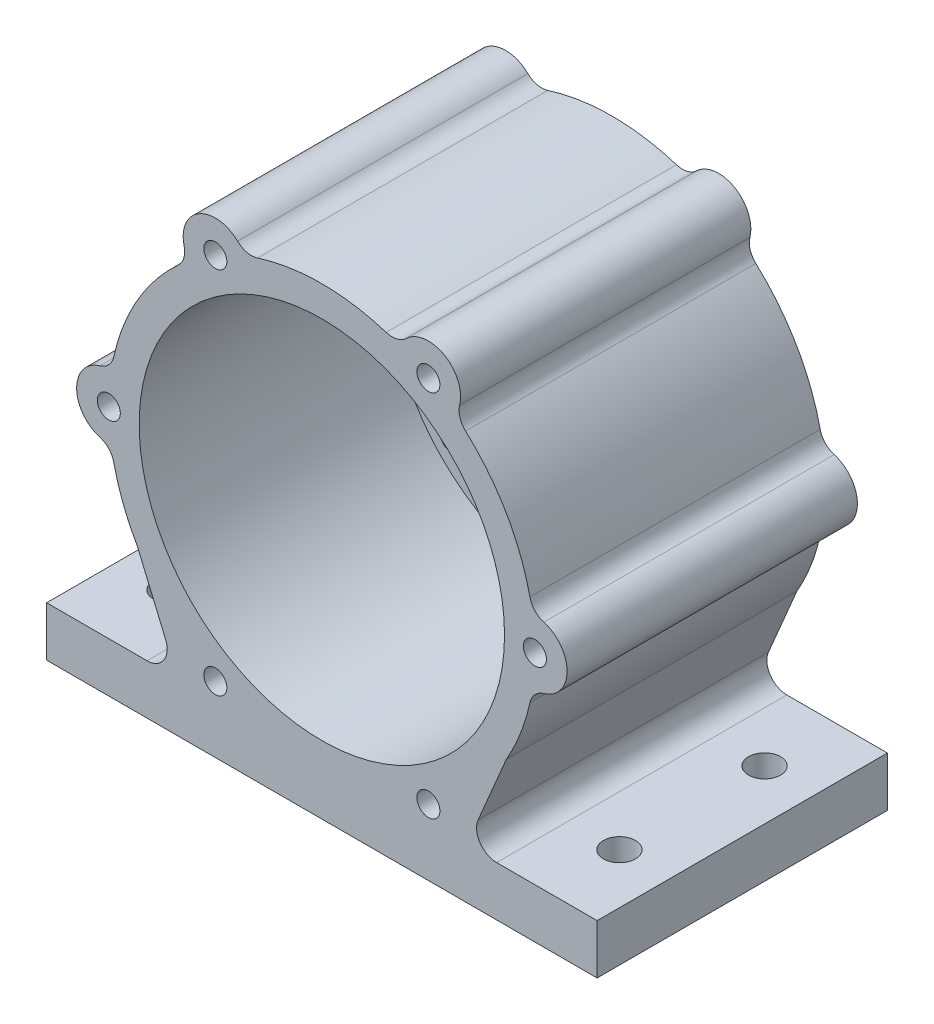
SolidWorks part; units mm, degrees
ref_plane "Front Plane" through (0, 0, 0) normal (0, 0, 1) x (1, 0, 0)
ref_plane "Top Plane" through (0, 0, 0) normal (0, 1, 0) x (1, 0, 0)
ref_plane "Right Plane" through (0, 0, 0) normal (1, 0, 0) x (0, 0, -1)
sketch "Sketch1" plane through (0, 0, 0) normal (0, 0, 1) x (1, 0, 0)
  line L0 (0, 0) -> (10.6425, 18.4334) construction
  line L1 (0, 0) -> (18.25, 0) construction
  circle A0 centre (0, 0) radius 21.285 construction
  circle A1 centre (0, 0) radius 18.25
  circle A2 centre (0, 0) radius 24.5
  circle A3 centre (10.6425, 18.4334) radius 1.15
  circle A4 centre (21.285, 0) radius 1.15
  circle A5 centre (10.6425, -18.4334) radius 1.15
  circle A6 centre (-10.6425, -18.4334) radius 1.15
  circle A7 centre (-21.285, 0) radius 1.15
  circle A8 centre (-10.6425, 18.4334) radius 1.15
  point P19 (0, 0)
  dimension "D1" = 49
  dimension "D2" = 36.5
  dimension "D3" = 42.57
  dimension "D4" = 2.3
  dimension "D6" = 60
  dimension "D5" = 6
extrude "Shell" add sketch "Sketch1" along normal blind 25
sketch "Sketch2" plane through (0, 0, 0) normal (0, 0, -1) x (-1, 0, 0)
  circle A0 centre (0, 0) radius 24.5 construction
  circle A1 centre (0, 0) radius 24.5
  circle A2 centre (0, 0) radius 7.25
  dimension "D1" = 14.5
extrude "Front Face" add sketch "Sketch2" along normal blind 4
sketch "Sketch3" plane through (0, 0, 0) normal (0, 0, 1) x (1, 0, 0)
  line L0 (2.9546, 10.8086) -> (4.278, 15.6446)
  line L1 (-3.0208, 10.8073) -> (-4.2915, 15.6527)
  line L2 (0, 0) -> (0, 17.25) construction
  line L3 (0, 17.25) -> (4.5502, 16.6391) construction
  line L4 (0, 17.25) -> (-4.5502, 16.6391) construction
  line L5 (10.8379, 2.8455) -> (15.6877, 4.1174)
  line L6 (7.849, 8.0197) -> (11.4099, 11.5429)
  line L7 (14.9389, 8.625) -> (16.6849, 4.379) construction
  line L8 (14.9389, 8.625) -> (12.1348, 12.2601) construction
  line L9 (7.8832, -7.9631) -> (11.4096, -11.5272)
  line L10 (10.8698, -2.7876) -> (15.7014, -4.1098)
  line L11 (14.9389, -8.625) -> (12.1348, -12.2601) construction
  line L12 (14.9389, -8.625) -> (16.6849, -4.379) construction
  line L13 (-2.9546, -10.8086) -> (-4.278, -15.6446)
  line L14 (3.0208, -10.8073) -> (4.2915, -15.6527)
  line L15 (0, -17.25) -> (-4.5502, -16.6391) construction
  line L16 (0, -17.25) -> (4.5502, -16.6391) construction
  line L17 (-10.8379, -2.8455) -> (-15.6877, -4.1174)
  line L18 (-7.849, -8.0197) -> (-11.4099, -11.5429)
  line L19 (-14.9389, -8.625) -> (-16.6849, -4.379) construction
  line L20 (-14.9389, -8.625) -> (-12.1348, -12.2601) construction
  line L21 (-7.8832, 7.9631) -> (-11.4096, 11.5272)
  line L22 (-10.8698, 2.7876) -> (-15.7014, 4.1098)
  line L23 (-14.9389, 8.625) -> (-12.1348, 12.2601) construction
  line L24 (-14.9389, 8.625) -> (-16.6849, 4.379) construction
  arc A0 (3.5174, 16.8876) -> (-3.5288, 16.8852) centre (0, 0) ccw
  arc A1 (1.8132, 10.0883) -> (-1.8709, 10.0778) centre (0, 0) ccw
  arc A2 (-3.0208, 10.8073) -> (-1.8709, 10.0778) centre (-2.0535, 11.061) ccw
  arc A3 (2.9546, 10.8086) -> (1.8132, 10.0883) centre (1.9901, 11.0726) cw
  arc A4 (4.278, 15.6446) -> (3.5174, 16.8876) centre (3.3135, 15.9086) ccw
  arc A5 (-4.2915, 15.6527) -> (-3.5288, 16.8852) centre (-3.3242, 15.9064) cw
  circle A6 centre (0, 0) radius 7.25 construction
  circle A7 centre (0, 0) radius 18.25 construction
  arc A8 (16.3838, 5.3976) -> (12.8586, 11.4986) centre (0, 0) ccw
  arc A9 (9.6434, 3.4739) -> (7.7922, 6.6592) centre (0, 0) ccw
  arc A10 (7.849, 8.0197) -> (7.7922, 6.6592) centre (8.5524, 7.3089) ccw
  arc A11 (10.8379, 2.8455) -> (9.6434, 3.4739) centre (10.5842, 3.8128) cw
  arc A12 (15.6877, 4.1174) -> (16.3838, 5.3976) centre (15.434, 5.0847) ccw
  arc A13 (11.4099, 11.5429) -> (12.8586, 11.4986) centre (12.1132, 10.832) cw
  arc A14 (12.8664, -11.49) -> (16.3874, -5.3866) centre (0, 0) ccw
  arc A15 (7.8302, -6.6145) -> (9.6631, -3.4186) centre (0, 0) ccw
  arc A16 (10.8698, -2.7876) -> (9.6631, -3.4186) centre (10.6058, -3.7521) ccw
  arc A17 (7.8832, -7.9631) -> (7.8302, -6.6145) centre (8.5941, -7.2598) cw
  arc A18 (11.4096, -11.5272) -> (12.8664, -11.49) centre (12.1205, -10.8239) ccw
  arc A19 (15.7014, -4.1098) -> (16.3874, -5.3866) centre (15.4374, -5.0743) cw
  arc A20 (-3.5174, -16.8876) -> (3.5288, -16.8852) centre (0, 0) ccw
  arc A21 (-1.8132, -10.0883) -> (1.8709, -10.0778) centre (0, 0) ccw
  arc A22 (3.0208, -10.8073) -> (1.8709, -10.0778) centre (2.0535, -11.061) ccw
  arc A23 (-2.9546, -10.8086) -> (-1.8132, -10.0883) centre (-1.9901, -11.0726) cw
  arc A24 (-4.278, -15.6446) -> (-3.5174, -16.8876) centre (-3.3135, -15.9086) ccw
  arc A25 (4.2915, -15.6527) -> (3.5288, -16.8852) centre (3.3242, -15.9064) cw
  arc A26 (-16.3838, -5.3976) -> (-12.8586, -11.4986) centre (0, 0) ccw
  arc A27 (-9.6434, -3.4739) -> (-7.7922, -6.6592) centre (0, 0) ccw
  arc A28 (-7.849, -8.0197) -> (-7.7922, -6.6592) centre (-8.5524, -7.3089) ccw
  arc A29 (-10.8379, -2.8455) -> (-9.6434, -3.4739) centre (-10.5842, -3.8128) cw
  arc A30 (-15.6877, -4.1174) -> (-16.3838, -5.3976) centre (-15.434, -5.0847) ccw
  arc A31 (-11.4099, -11.5429) -> (-12.8586, -11.4986) centre (-12.1132, -10.832) cw
  arc A32 (-12.8664, 11.49) -> (-16.3874, 5.3866) centre (0, 0) ccw
  arc A33 (-7.8302, 6.6145) -> (-9.6631, 3.4186) centre (0, 0) ccw
  arc A34 (-10.8698, 2.7876) -> (-9.6631, 3.4186) centre (-10.6058, 3.7521) ccw
  arc A35 (-7.8832, 7.9631) -> (-7.8302, 6.6145) centre (-8.5941, 7.2598) cw
  arc A36 (-11.4096, 11.5272) -> (-12.8664, 11.49) centre (-12.1205, 10.8239) ccw
  arc A37 (-15.7014, 4.1098) -> (-16.3874, 5.3866) centre (-15.4374, 5.0743) cw
  point P98 (0, 0)
  dimension "D2" = 1
  dimension "D3" = 3
  dimension "D4" = 1
  dimension "D1" = 30
  dimension "D5" = 6
extrude "Front Cutout" cut sketch "Sketch3" against normal up to next
sketch "Sketch4" plane through (0, 0, 25) normal (0, 0, 1) x (1, 0, 0)
  arc A0 (-14.3579, 15.7131) -> (-20.7869, 4.5777) centre (0, 0) ccw
  arc A1 (-8.4173, 20.7539) -> (-13.7647, 17.6666) centre (-10.6425, 18.4334) ccw
  arc A2 (13.7647, 17.6666) -> (8.4173, 20.7539) centre (10.6425, 18.4334) ccw
  arc A3 (22.1821, -3.0873) -> (22.1821, 3.0873) centre (21.285, 0) ccw
  arc A4 (8.4173, -20.7539) -> (13.7647, -17.6666) centre (10.6425, -18.4334) ccw
  arc A5 (-13.7647, -17.6666) -> (-8.4173, -20.7539) centre (-10.6425, -18.4334) ccw
  arc A6 (-22.1821, 3.0873) -> (-22.1821, -3.0873) centre (-21.285, 0) ccw
  arc A7 (6.429, 20.2909) -> (-6.429, 20.2909) centre (0, 0) ccw
  arc A8 (-20.7869, -4.5777) -> (-14.3579, -15.7131) centre (0, 0) ccw
  arc A9 (-6.429, -20.2909) -> (6.429, -20.2909) centre (0, 0) ccw
  arc A10 (14.3579, -15.7131) -> (20.7869, -4.5777) centre (0, 0) ccw
  arc A11 (20.7869, 4.5777) -> (14.3579, 15.7131) centre (0, 0) ccw
  arc A12 (-6.429, 20.2909) -> (-8.4173, 20.7539) centre (-7.0331, 22.1974) cw
  arc A13 (8.4173, 20.7539) -> (6.429, 20.2909) centre (7.0331, 22.1974) cw
  arc A14 (13.7647, 17.6666) -> (14.3579, 15.7131) centre (15.707, 17.1896) ccw
  arc A15 (22.1821, 3.0873) -> (20.7869, 4.5777) centre (22.7401, 5.0079) cw
  arc A16 (22.1821, -3.0873) -> (20.7869, -4.5777) centre (22.7401, -5.0079) ccw
  arc A17 (13.7647, -17.6666) -> (14.3579, -15.7131) centre (15.707, -17.1896) cw
  arc A18 (8.4173, -20.7539) -> (6.429, -20.2909) centre (7.0331, -22.1974) ccw
  arc A19 (-8.4173, -20.7539) -> (-6.429, -20.2909) centre (-7.0331, -22.1974) cw
  arc A20 (-13.7647, -17.6666) -> (-14.3579, -15.7131) centre (-15.707, -17.1896) ccw
  arc A21 (-22.1821, -3.0873) -> (-20.7869, -4.5777) centre (-22.7401, -5.0079) cw
  arc A22 (-22.1821, 3.0873) -> (-20.7869, 4.5777) centre (-22.7401, 5.0079) ccw
  arc A23 (-14.3579, 15.7131) -> (-13.7647, 17.6666) centre (-15.707, 17.1896) ccw
  circle A24 centre (0, 0) radius 47.6629
  point P24 (0, 0)
  dimension "D2" = 2
  dimension "D1" = 6
extrude "Cut-Extrude2" cut sketch "Sketch4" against normal through all
sketch "Sketch5" plane through (0, 0, 25) normal (0, 0, 1) x (1, 0, 0)
  line L0 (-27.5, -25.0363) -> (27.5, -25.0363)
  line L1 (0, -10.6425) -> (0, -25.0363) construction
  line L2 (-18.4334, -10.6425) -> (18.4334, -10.6425) construction
  line L3 (27.5, -25.0363) -> (27.5, -20.0708)
  line L4 (27.5, -20.0708) -> (17.4562, -20.0708)
  line L5 (15.6148, -17.2901) -> (18.4334, -10.6425)
  line L6 (-15.6148, -17.2901) -> (-18.4334, -10.6425)
  line L7 (-27.5, -20.0708) -> (-17.4562, -20.0708)
  line L8 (-27.5, -25.0363) -> (-27.5, -20.0708)
  arc A0 (-20.7869, -4.5777) -> (-14.3579, -15.7131) centre (0, 0) ccw construction
  arc A1 (17.4562, -20.0708) -> (15.6148, -17.2901) centre (17.4562, -18.0708) cw
  arc A2 (-17.4562, -20.0708) -> (-15.6148, -17.2901) centre (-17.4562, -18.0708) ccw
  arc A25 (20.7869, 4.5777) -> (14.3579, 15.7131) centre (0, 0) ccw
  arc A26 (13.7647, 17.6666) -> (14.3579, 15.7131) centre (15.707, 17.1896) ccw
  arc A27 (13.7647, 17.6666) -> (8.4173, 20.7539) centre (10.6425, 18.4334) ccw
  arc A28 (6.429, 20.2909) -> (8.4173, 20.7539) centre (7.0331, 22.1974) ccw
  arc A29 (6.429, 20.2909) -> (-6.429, 20.2909) centre (0, 0) ccw
  arc A30 (-8.4173, 20.7539) -> (-6.429, 20.2909) centre (-7.0331, 22.1974) ccw
  arc A31 (-8.4173, 20.7539) -> (-13.7647, 17.6666) centre (-10.6425, 18.4334) ccw
  arc A32 (-14.3579, 15.7131) -> (-13.7647, 17.6666) centre (-15.707, 17.1896) ccw
  arc A33 (-14.3579, 15.7131) -> (-20.7869, 4.5777) centre (0, 0) ccw
  arc A34 (-22.1821, 3.0873) -> (-20.7869, 4.5777) centre (-22.7401, 5.0079) ccw
  arc A35 (-22.1821, 3.0873) -> (-22.1821, -3.0873) centre (-21.285, 0) ccw
  arc A36 (-20.7869, -4.5777) -> (-22.1821, -3.0873) centre (-22.7401, -5.0079) ccw
  arc A37 (-20.7869, -4.5777) -> (-14.3579, -15.7131) centre (0, 0) ccw
  arc A38 (-13.7647, -17.6666) -> (-14.3579, -15.7131) centre (-15.707, -17.1896) ccw
  arc A39 (-13.7647, -17.6666) -> (-8.4173, -20.7539) centre (-10.6425, -18.4334) ccw
  arc A40 (-6.429, -20.2909) -> (-8.4173, -20.7539) centre (-7.0331, -22.1974) ccw
  arc A41 (-6.429, -20.2909) -> (6.429, -20.2909) centre (0, 0) ccw
  arc A42 (8.4173, -20.7539) -> (6.429, -20.2909) centre (7.0331, -22.1974) ccw
  arc A43 (8.4173, -20.7539) -> (13.7647, -17.6666) centre (10.6425, -18.4334) ccw
  arc A44 (14.3579, -15.7131) -> (13.7647, -17.6666) centre (15.707, -17.1896) ccw
  arc A45 (14.3579, -15.7131) -> (20.7869, -4.5777) centre (0, 0) ccw
  arc A46 (22.1821, -3.0873) -> (20.7869, -4.5777) centre (22.7401, -5.0079) ccw
  arc A47 (22.1821, -3.0873) -> (22.1821, 3.0873) centre (21.285, 0) ccw
  arc A48 (20.7869, 4.5777) -> (22.1821, 3.0873) centre (22.7401, 5.0079) ccw
  arc A61 (-18.4334, -10.6425) -> (-14.3579, -15.7131) centre (0, 0) ccw
  arc A62 (-13.7647, -17.6666) -> (-14.3579, -15.7131) centre (-15.707, -17.1896) ccw
  arc A63 (-13.7647, -17.6666) -> (-8.4173, -20.7539) centre (-10.6425, -18.4334) ccw
  arc A64 (-6.429, -20.2909) -> (-8.4173, -20.7539) centre (-7.0331, -22.1974) ccw
  arc A65 (-6.429, -20.2909) -> (6.429, -20.2909) centre (0, 0) ccw
  arc A66 (8.4173, -20.7539) -> (6.429, -20.2909) centre (7.0331, -22.1974) ccw
  arc A67 (8.4173, -20.7539) -> (13.7647, -17.6666) centre (10.6425, -18.4334) ccw
  arc A68 (14.3579, -15.7131) -> (13.7647, -17.6666) centre (15.707, -17.1896) ccw
  arc A69 (14.3579, -15.7131) -> (18.4334, -10.6425) centre (0, 0) ccw
  dimension "D2" = 2
  dimension "D3" = 55
  dimension "D1" = 0
extrude "Foot" add sketch "Sketch5" against normal up to surface (29 mm away) up to face at (11.6209, -6.6879, -4)
sketch "Sketch6" plane through (0, -20.0708, 0) normal (0, 1, 0) x (1, 0, 0)
  line L0 (22.4781, -25) -> (22.4781, -17.75) construction
  line L1 (27.5, -25) -> (17.4562, -25) construction
  line L2 (22.4781, -17.75) -> (22.4781, -10.5) construction
  line L3 (22.4781, -10.5) -> (22.4781, -3.25) construction
  line L4 (22.4781, -3.25) -> (22.4781, 4) construction
  line L5 (27.5, 4) -> (17.4562, 4) construction
  line L6 (-27.5, -25) -> (27.5, -25) construction
  line L7 (-27.5, -25) -> (27.5, -25) construction
  line L8 (0, -25) -> (0, -4.7747) construction
  circle A0 centre (22.4781, -17.75) radius 1.6
  circle A1 centre (22.4781, -3.25) radius 1.6
  circle A2 centre (-22.4781, -17.75) radius 1.6
  circle A3 centre (-22.4781, -3.25) radius 1.6
  dimension "D1" = 3.2
extrude "Cut-Extrude3" cut sketch "Sketch6" against normal up to next
